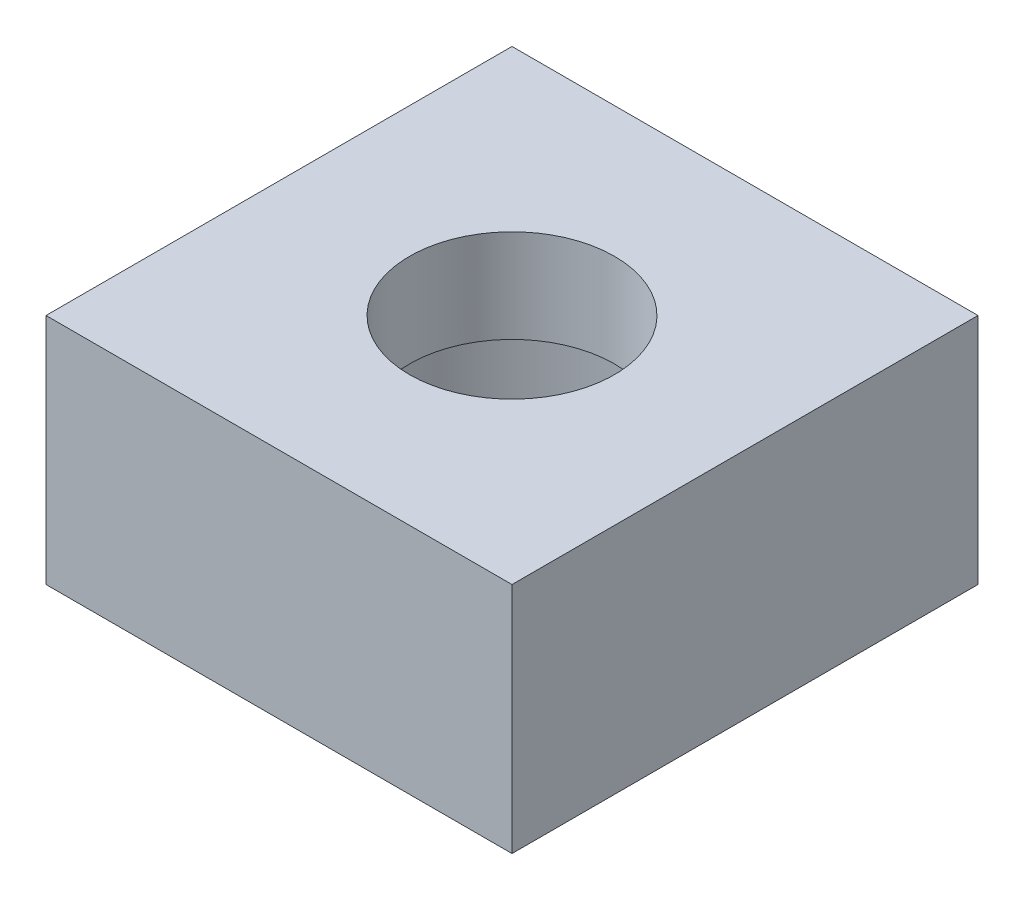
SolidWorks part; units mm, degrees
ref_plane "Front Plane" through (0, 0, 0) normal (0, 0, 1) x (1, 0, 0)
ref_plane "Top Plane" through (0, 0, 0) normal (0, 1, 0) x (1, 0, 0)
ref_plane "Right Plane" through (0, 0, 0) normal (1, 0, 0) x (0, 0, -1)
sketch "Sketch1" plane through (0, 0, 0) normal (0, 1, 0) x (1, 0, 0)
  line L1 (-5, 5) -> (5, 5)
  line L2 (-5, 5) -> (-5, -5)
  line L3 (-5, -5) -> (5, -5)
  line L4 (5, 5) -> (5, -5)
  line L5 (-5, 5) -> (5, -5) construction
  line L6 (-5, -5) -> (5, 5) construction
  circle A0 centre (0, 0) radius 2.2
  circle A1 centre (0, 0) radius 4
  dimension "D1" = 4.4
  dimension "D2" = 8
  dimension "D3" = 10
  dimension "D4" = 10
extrude "Boss-Extrude1" add sketch "Sketch1" along normal blind 5 contours A1 A0 | L4 L1 L2 L3 A1
sketch "Sketch3" plane through (0, 0, 0) normal (0, -1, 0) x (1, 0, 0)
  line L4 (5, -5) -> (5, 5)
  line L5 (5, 5) -> (-5, 5)
  line L6 (-5, 5) -> (-5, -5)
  line L7 (-5, -5) -> (5, -5)
  line L8 (5, -5) -> (5, 5)
  line L9 (5, 5) -> (-5, 5)
  line L10 (-5, 5) -> (-5, -5)
  line L11 (-5, -5) -> (5, -5)
  circle A0 centre (0, 0) radius 4
  circle M6 centre (0, 0) radius 2.2
  dimension "D2" = 8
  dimension "D1" = 0
extrude "Cut-Extrude3" cut sketch "Sketch3" against normal blind 3 contours A0 M6
